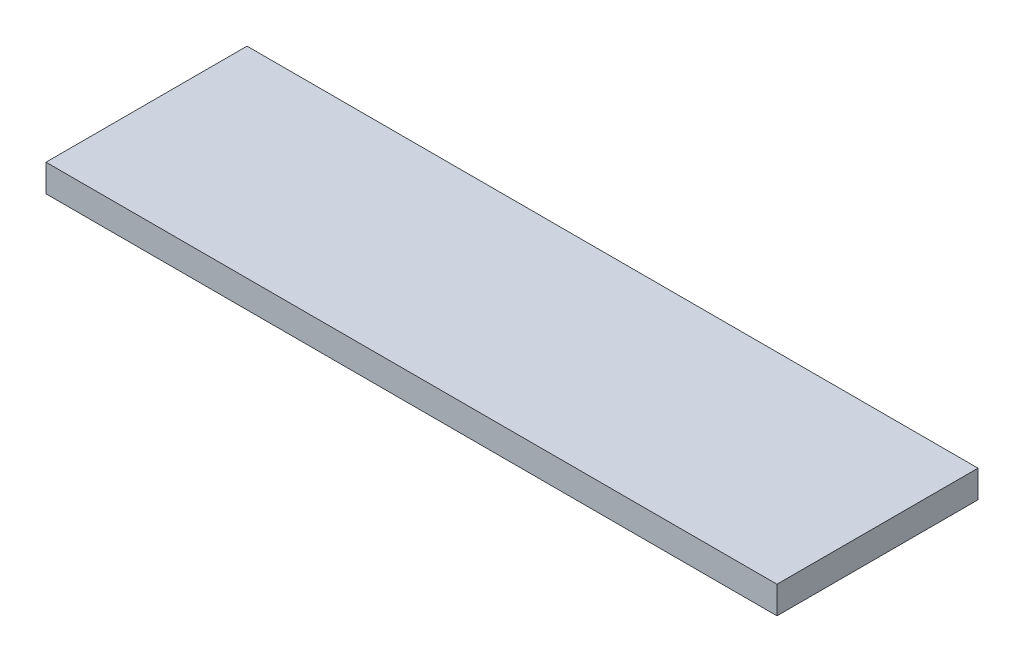
SolidWorks part; units mm, degrees
ref_plane "Front Plane" through (0, 0, 0) normal (0, 0, 1) x (1, 0, 0)
ref_plane "Top Plane" through (0, 0, 0) normal (0, 1, 0) x (1, 0, 0)
ref_plane "Right Plane" through (0, 0, 0) normal (1, 0, 0) x (0, 0, -1)
sketch "Sketch2" plane through (0, 0, 0) normal (0, 1, 0) x (1, 0, 0)
  line L1 (-508, 139.7) -> (508, 139.7)
  line L2 (-508, 139.7) -> (-508, -139.7)
  line L3 (-508, -139.7) -> (508, -139.7)
  line L4 (508, 139.7) -> (508, -139.7)
  line L5 (-508, 139.7) -> (508, -139.7) construction
  line L6 (-508, -139.7) -> (508, 139.7) construction
  point P0 (0, 0)
  dimension "D1" = 1016
  dimension "D2" = 279.4
extrude "Boss-Extrude1" add sketch "Sketch2" along normal blind 38.1
